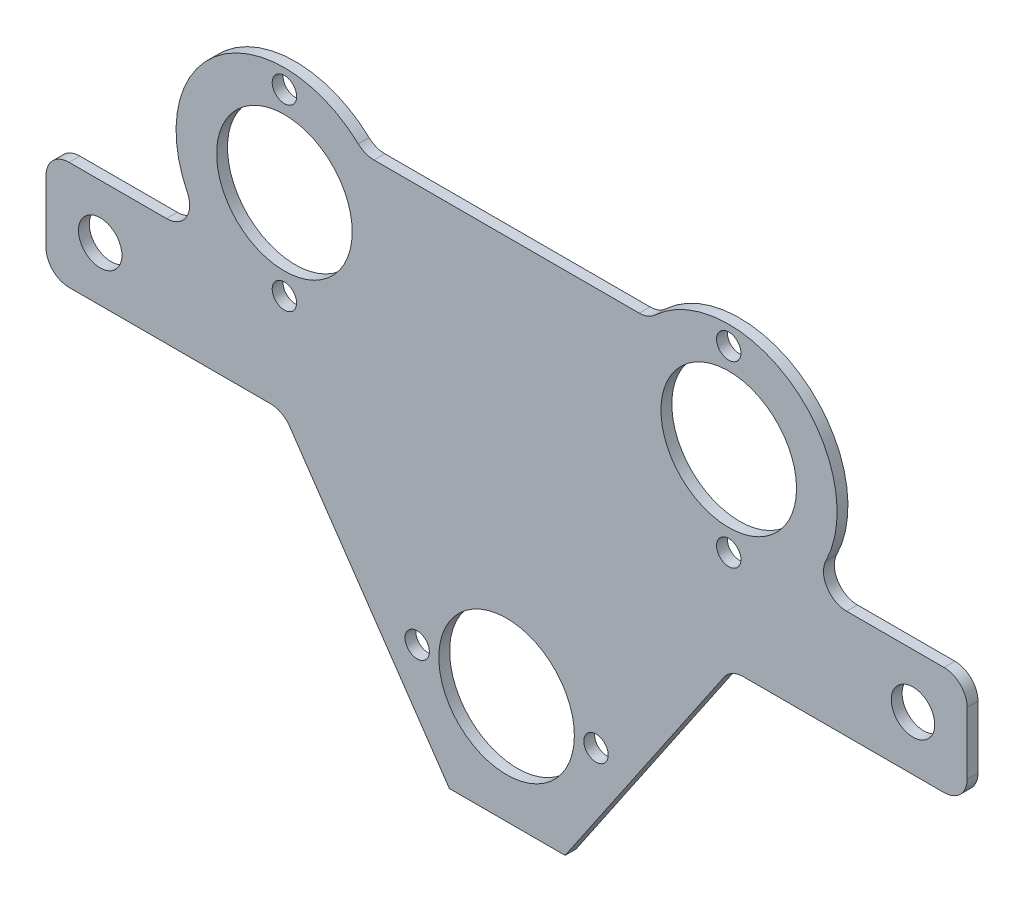
SolidWorks part; units mm, degrees
ref_plane "Front Plane" through (0, 0, 0) normal (0, 0, 1) x (1, 0, 0)
ref_plane "Top Plane" through (0, 0, 0) normal (0, 1, 0) x (1, 0, 0)
ref_plane "Right Plane" through (0, 0, 0) normal (1, 0, 0) x (0, 0, -1)
sketch "Sketch1" plane through (0, 0, 0) normal (0, 0, 1) x (1, 0, 0)
  line L0 (-75, 0) -> (75, 0) construction
  line L9 (-10.5568, -55) -> (10.8054, -55)
  line L10 (-26.2436, 38.5) -> (26.2436, 38.5)
  line L11 (-85, 10) -> (85, 10)
  line L12 (-85, 10) -> (-85, -10)
  line L13 (-85, -10) -> (85, -10)
  line L14 (85, 10) -> (85, -10)
  line L16 (0, 45) -> (0, -1.1695) construction
  line L21 (-41, 25) -> (0, -35) construction
  line L22 (0, -35) -> (41, 25) construction
  line L23 (41, 25) -> (-41, 25) construction
  line L24 (-10.5568, -55) -> (-57.5129, 13.7162)
  line L25 (10.8054, -55) -> (57.3846, 13.5308)
  circle A3 centre (-75, 0) radius 4.01
  circle A4 centre (-41, 25) radius 12.51
  circle A5 centre (41, 25) radius 12.51
  circle A6 centre (0, -35) radius 12.51
  circle A7 centre (-41, 25) radius 20
  circle A8 centre (41, 25) radius 20
  circle A24 centre (0, -35) radius 20
  circle A25 centre (75, 0) radius 4.01
  point P9 (0, -10)
  point P10 (-85, 0)
  point P11 (0, 0)
  dimension "D12" = 25.02
  dimension "D16" = 40
  dimension "D5" = 8.02
  dimension "D2" = 10
  dimension "D3" = 85
  dimension "D4" = 75
  dimension "D13" = 41
  dimension "D14" = 25
  dimension "D15" = 35
extrude "Boss-Extrude1" add sketch "Sketch1" along normal blind 2
fillet "Fillet1" radius 4.25 10 edges at (-85, -10, 1) (-85, 10, 1) (85, -10, 1) (85, 10, 1) (54.9848, 10, 1) (-54.9735, 10, 1) (41.3912, -10, 1) (-41.3068, -10, 1) (26.2436, 38.5, 1) (-26.2436, 38.5, 1)
sketch "Sketch2" plane through (0, 0, 2) normal (0, 0, 1) x (1, 0, 0)
  circle A0 centre (-41, 25) radius 16.5 construction
  circle A1 centre (-41, 41.5) radius 2.25
  circle A3 centre (-41, 8.5) radius 2.25
  circle A5 centre (41, 25) radius 16.5 construction
  circle A8 centre (0, -35) radius 16.5 construction
  circle A9 centre (-24.5, 25) radius 2.25 [skipped]
  circle A10 centre (-57.5, 25) radius 2.25 [skipped]
  circle A11 centre (-16.5, -35) radius 2.25
  circle A12 centre (16.5, -35) radius 2.25
  circle A13 centre (41, 8.5) radius 2.25
  circle A14 centre (41, 41.5) radius 2.25
  point P14 (-41, 25)
  dimension "D1" = 33
  dimension "D2" = 4.5
  dimension "D3" = 4
extrude "Cut-Extrude1" cut sketch "Sketch2" against normal up to next
